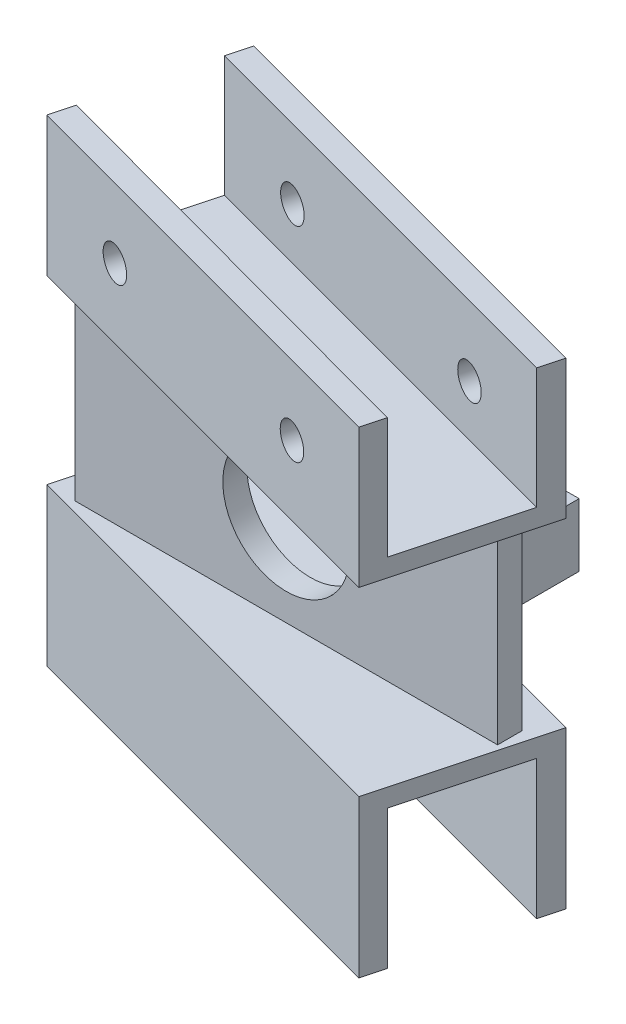
SolidWorks part; units mm, degrees
ref_plane "Front Plane" through (0, 0, 0) normal (0, 0, 1) x (1, 0, 0)
ref_plane "Top Plane" through (0, 0, 0) normal (0, 1, 0) x (1, 0, 0)
ref_plane "Right Plane" through (0, 0, 0) normal (1, 0, 0) x (0, 0, -1)
sketch "Sketch1" plane through (0, 0, 0) normal (0, 0, 1) x (1, 0, 0)
  line L1 (0, 0) -> (70, 0)
  line L2 (0, 0) -> (0, -30)
  line L3 (0, -30) -> (70, -30)
  line L4 (70, 0) -> (70, -30)
  circle A0 centre (35, -15) radius 10.5
  point P7 (70, -15)
  point P8 (35, -30)
  dimension "D1" = 21
  dimension "D2" = 30
  dimension "D3" = 70
extrude "Boss-Extrude1" add sketch "Sketch1" along normal blind 4
sketch "Sketch3" plane through (0, 0, 0) normal (0, 0, -1) x (-1, 0, 0)
  line L0 (-62.5, -8.9384) -> (-54.349, -8.9384)
  line L1 (-54.349, -8.9384) -> (-54.349, -19.3738)
  line L2 (-54.349, -19.3738) -> (-62.5, -19.3738)
  line L3 (-7.5, -5) -> (-14.3209, -5)
  line L4 (-7.5, -25) -> (-7.5, -5)
  line L5 (-62.5, -25) -> (-7.5, -25)
  line L6 (-62.5, -5) -> (-62.5, -25)
  line L7 (-7.5, -5) -> (-62.5, -5)
  line L8 (-7.5, -25) -> (-7.5, -5)
  line L10 (-62.5, -8.9384) -> (-62.5, -19.3738)
  line L12 (-14.3209, -5) -> (-14.3209, -25)
  line L13 (-14.3209, -25) -> (-7.5, -25)
  dimension "D1" = 0
extrude "Boss-Extrude2" add sketch "Sketch3" along normal blind 17
sketch "Sketch4" plane through (0, 0, -17) normal (0, 0, -1) x (-1, 0, 0)
  circle A0 centre (-58.5, -14.2891) radius 1 construction
  circle A1 centre (-58.5, -14.2891) radius 1
  circle A2 centre (-11.5, -7) radius 1 construction
  circle A3 centre (-11.5, -7) radius 1
  circle A4 centre (-11.5, -23) radius 1 construction
  circle A5 centre (-11.5, -23) radius 1
extrude "Cut-Extrude1" cut sketch "Sketch4" against normal blind 17
sketch "Sketch7" plane through (0, 0, 0) normal (0, 1, 0) x (1, 0, 0)
  line L1 (-4.6304, -4) -> (65.9508, -22.9122)
  line L2 (65.9508, -22.9122) -> (73.1977, 4.1338)
  line L5 (-4.6304, -4) -> (2.6166, 23.0459)
  line L8 (70, -4) -> (0, -4) construction
  line L9 (73.1977, 4.1338) -> (2.6166, 23.0459)
  dimension "D1" = 28
  dimension "D2" = 15
extrude "Boss-Extrude4" add sketch "Sketch7" along normal blind 3
sketch "Sketch9" plane through (0, 3, 0) normal (0, 1, 0) x (1, 0, 0)
  line L0 (-4.6304, -4) -> (65.9508, -22.9122)
  line L1 (65.9508, -22.9122) -> (66.944, -19.2056)
  line L2 (65.9508, -22.9122) -> (73.1977, 4.1338) construction
  line L3 (66.944, -19.2056) -> (-3.5951, -0.1363)
  line L4 (2.6166, 23.0459) -> (-4.6304, -4) construction
  line L5 (-3.5951, -0.1363) -> (-4.6304, -4)
  line L6 (2.6166, 23.0459) -> (1.5813, 19.1822)
  line L7 (1.5813, 19.1822) -> (72.1624, 0.2701)
  line L8 (72.1624, 0.2701) -> (73.1977, 4.1338)
  line L9 (73.1977, 4.1338) -> (2.6166, 23.0459)
  dimension "D1" = 4
  dimension "D2" = 4
extrude "Boss-Extrude5" add sketch "Sketch9" along normal blind 20
sketch "Sketch10" plane through (5.9368, 0, -22.1563) normal (0.2588, 0, -0.9659) x (-0.9659, 0, -0.2588)
  line L0 (-69.6337, 23) -> (-69.6337, 0) construction
  circle A0 centre (-53.9537, 11.5) radius 2.75
  circle A1 centre (-12.4883, 11.5) radius 2.75
  point P6 (-69.6337, 11.5)
  dimension "D1" = 5.5
  dimension "D2" = 5.5
extrude "Cut-Extrude2" cut sketch "Sketch10" against normal through all
sketch "Sketch5" plane through (0, -30, 0) normal (0, -1, 0) x (1, 0, 0)
  line L5 (-4.6304, 4) -> (2.6166, -23.0459)
  line L6 (2.6166, -23.0459) -> (73.1977, -4.1338)
  line L7 (73.1977, -4.1338) -> (65.9508, 22.9122)
  line L8 (65.9508, 22.9122) -> (-4.6304, 4)
  line L9 (-4.6304, 4) -> (2.6166, -23.0459)
  line L10 (2.6166, -23.0459) -> (73.1977, -4.1338)
  line L11 (73.1977, -4.1338) -> (65.9508, 22.9122)
  line L12 (65.9508, 22.9122) -> (-4.6304, 4)
  dimension "D1" = 0
extrude "Boss-Extrude6" add sketch "Sketch5" along normal blind 3
sketch "Sketch6" plane through (0, -33, 0) normal (0, -1, 0) x (1, 0, 0)
  line L4 (-4.6304, 4) -> (-3.5951, 0.1363)
  line L5 (65.9508, 22.9122) -> (-4.6304, 4)
  line L6 (66.944, 19.2056) -> (65.9508, 22.9122)
  line L7 (-3.5951, 0.1363) -> (66.944, 19.2056)
  line L8 (-4.6304, 4) -> (-3.5951, 0.1363)
  line L9 (65.9508, 22.9122) -> (-4.6304, 4)
  line L10 (66.944, 19.2056) -> (65.9508, 22.9122)
  line L11 (-3.5951, 0.1363) -> (66.944, 19.2056)
  line L12 (2.6166, -23.0459) -> (73.1977, -4.1338)
  line L13 (1.5813, -19.1822) -> (2.6166, -23.0459)
  line L14 (72.1624, -0.2701) -> (1.5813, -19.1822)
  line L15 (73.1977, -4.1338) -> (72.1624, -0.2701)
  line L16 (2.6166, -23.0459) -> (73.1977, -4.1338)
  line L17 (1.5813, -19.1822) -> (2.6166, -23.0459)
  line L18 (72.1624, -0.2701) -> (1.5813, -19.1822)
  line L19 (73.1977, -4.1338) -> (72.1624, -0.2701)
  dimension "D1" = 0
  dimension "D2" = 0
extrude "Boss-Extrude7" add sketch "Sketch6" along normal blind 23
sketch "Sketch8" plane through (-1.3102, 0, 4.8896) normal (-0.2588, 0, 0.9659) x (0.9659, 0, 0.2588)
  circle A0 centre (54.7991, -45.4167) radius 2.75
  circle A1 centre (21.292, -45.4167) radius 2.75
  point P4 (0, 0)
  point P7 (0, 0)
  dimension "D1" = 5.5
  dimension "D2" = 5.5
